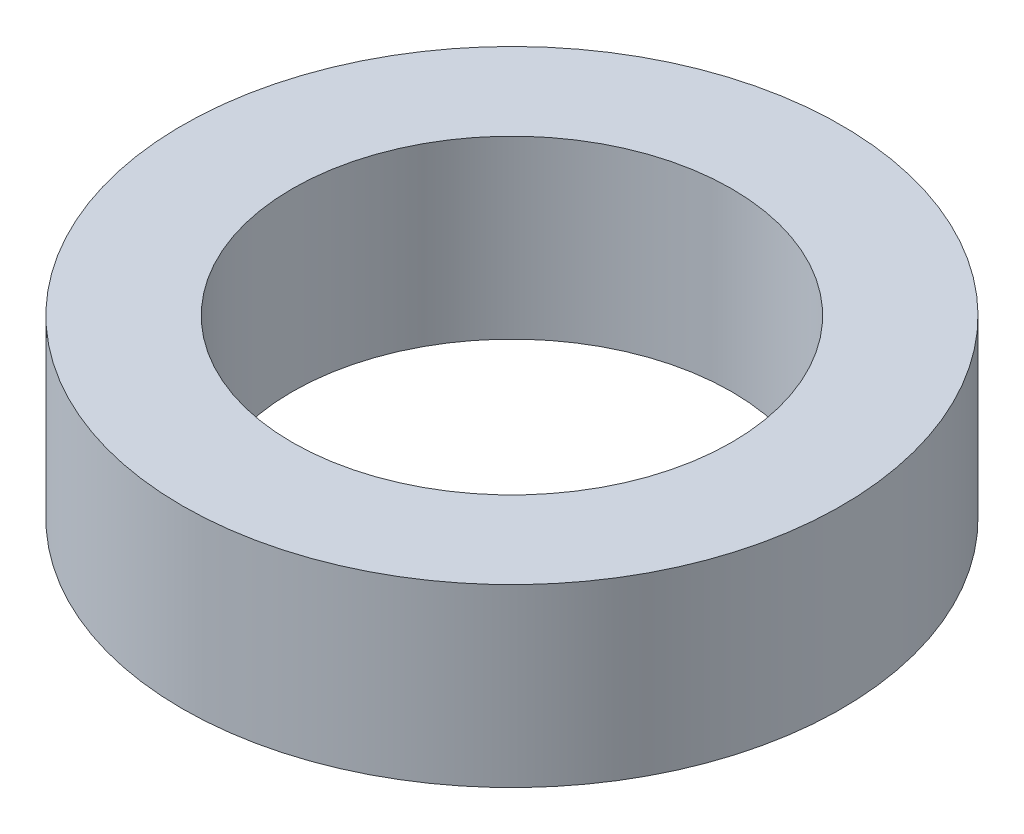
SolidWorks part; units mm, degrees
ref_plane "前视基准面" through (0, 0, 0) normal (0, 0, 1) x (1, 0, 0)
ref_plane "上视基准面" through (0, 0, 0) normal (0, 1, 0) x (1, 0, 0)
ref_plane "右视基准面" through (0, 0, 0) normal (1, 0, 0) x (0, 0, -1)
sketch "草图1" plane through (0, 0, 0) normal (0, 1, 0) x (1, 0, 0)
  circle A0 centre (0, 0) radius 5
  circle A1 centre (0, 0) radius 7.5
  dimension "D1" = 10
  dimension "D2" = 15
extrude "凸台-拉伸1" add sketch "草图1" along normal blind 4
